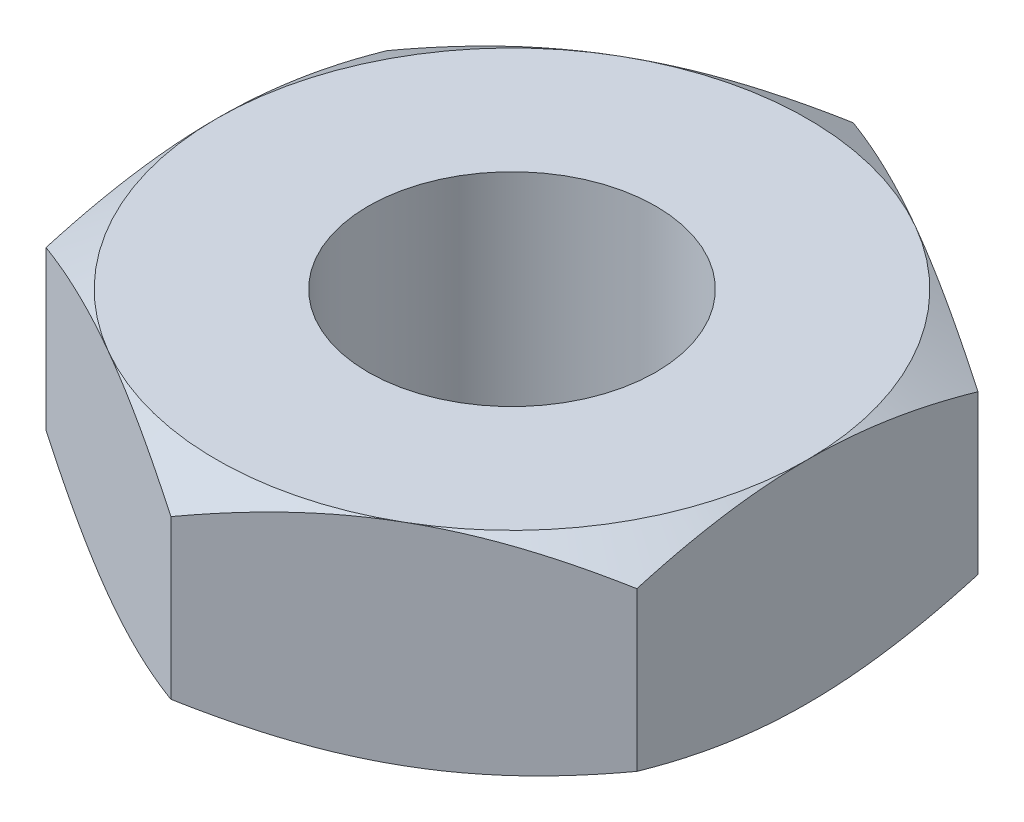
SolidWorks part; units mm, degrees
material "AISI 4130 Steel, normalized at 870C"
ref_plane "Front Plane" through (0, 0, 0) normal (0, 0, 1) x (1, 0, 0)
ref_plane "Top Plane" through (0, 0, 0) normal (0, 1, 0) x (1, 0, 0)
ref_plane "Right Plane" through (0, 0, 0) normal (1, 0, 0) x (0, 0, -1)
sketch "Sketch1" plane through (0, 0, 0) normal (0, 1, 0) x (1, 0, 0)
  line L1 (-5.5563, 3.2079) -> (-5.5563, -3.2079)
  line L2 (-5.5563, -3.2079) -> (0, -6.4158)
  line L3 (0, -6.4158) -> (5.5562, -3.2079)
  line L4 (5.5562, -3.2079) -> (5.5562, 3.2079)
  line L5 (5.5562, 3.2079) -> (0, 6.4158)
  line L6 (0, 6.4158) -> (-5.5563, 3.2079)
  circle A0 centre (0, 0) radius 5.5563 construction
  dimension "Hex" = 11.1125
extrude "Boss-Extrude1" add sketch "Sketch1" along normal mid plane 3.9688
hole_wizard "1/4-28 Tapped Hole1" positions "Sketch6" profile "Sketch7" tap size "1/4-28" standard "ANSI Inch" end condition through all
sketch "Sketch6" plane through (0, 1.9844, 0) normal (0, 1, 0) x (1, 0, 0)
  point P0 (0, 0)
sketch "Sketch7" plane through (0, 1.9844, 0) normal (1, 0, 0) x (0, 0, 1)
  line L0 (0, 0) -> (0, 3.9688)
  line L1 (0, 3.9688) -> (2.7051, 3.9688)
  line L2 (2.7051, 3.9688) -> (2.7051, 0)
  line L5 (2.7051, 0) -> (0, 0)
  line L11 (0, -6.35) -> (0, 107.95) construction
  dimension "Thru Tap Drill Dia." = 5.4102
  dimension "Thru Tap Drill Depth" = 3.9688
cosmetic thread "Hole Thread1" parameters "D2"=6.35
sketch "Sketch5" plane through (0, 1.9844, 0) normal (0, 1, 0) x (1, 0, 0)
  circle A0 centre (0, 0) radius 5.5563 construction
  circle A1 centre (0, 0) radius 5.5563
extrude "Cut-Extrude2" cut sketch "Sketch5" against normal through all draft 60 flip side to cut
mirror "Mirror1" about plane through (0, 0, 0) normal (0, 1, 0) of "Cut-Extrude2"
